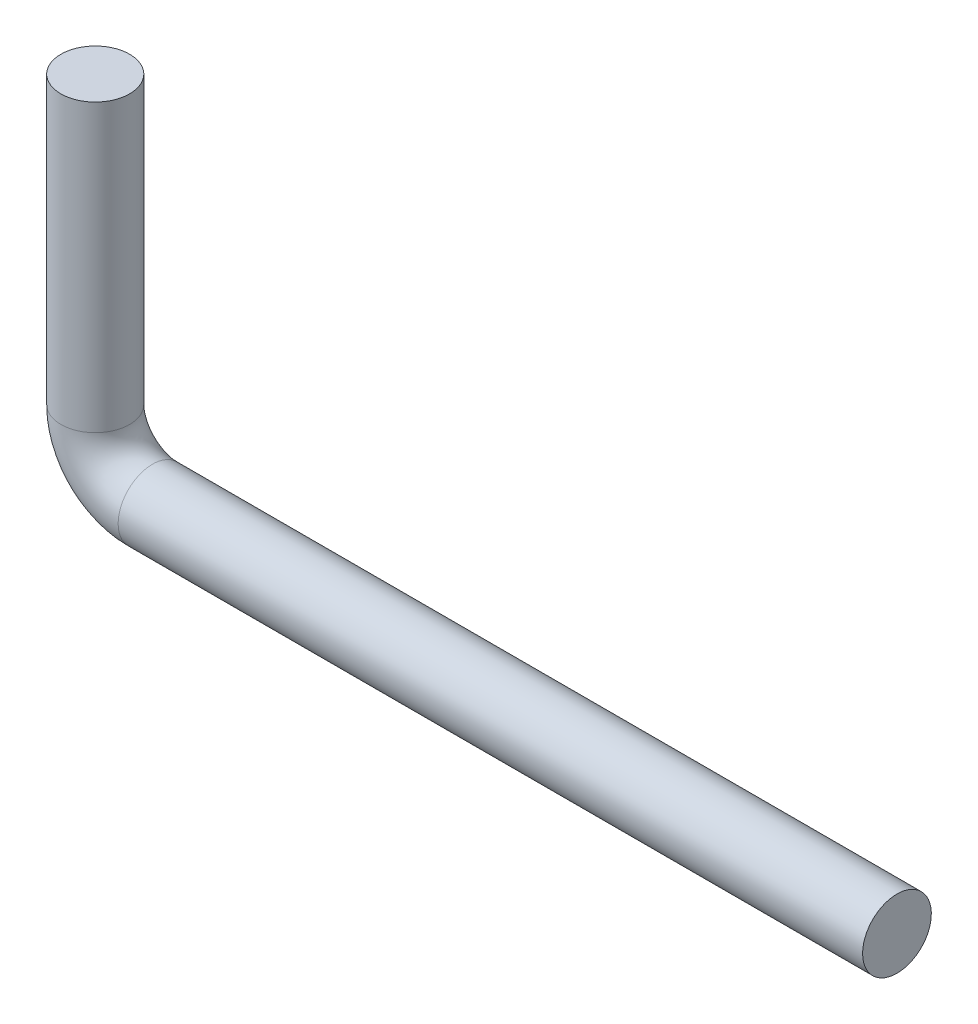
SolidWorks part; units mm, degrees
ref_plane "Front" through (0, 0, 0) normal (0, 0, 1) x (1, 0, 0)
ref_plane "Top" through (0, 0, 0) normal (0, 1, 0) x (1, 0, 0)
ref_plane "Right" through (0, 0, 0) normal (1, 0, 0) x (0, 0, -1)
ref_plane "Plane1" through (0, 60, 0) normal (0, 1, 0) x (1, 0, 0)
sketch "Sketch3" plane through (0, 0, 0) normal (0, 0, 1) x (1, 0, 0)
  line L0 (0, 60) -> (0, 10)
  line L1 (50, 60) -> (-50, 60) construction
  line L2 (10, 0) -> (140, 0)
  arc A0 (0, 10) -> (10, 0) centre (10, 10) ccw
  point P8 (0, 0)
  dimension "D1" = 10
  dimension "D2" = 130
sketch "Sketch4" plane through (0, 60, 0) normal (0, 1, 0) x (1, 0, 0)
  circle A0 centre (0, 0) radius 6
sweep "Sweep1" add profiles "Sketch4" path "Sketch3"
